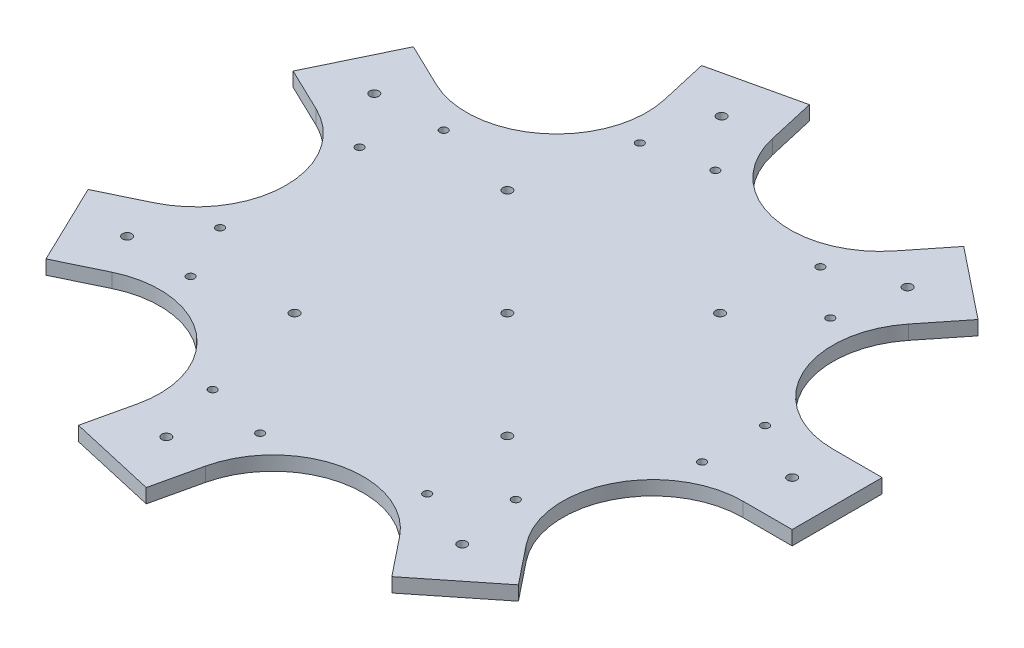
SolidWorks part; units mm, degrees
ref_plane "Front Plane" through (0, 0, 0) normal (0, 0, 1) x (1, 0, 0)
ref_plane "Top Plane" through (0, 0, 0) normal (0, 1, 0) x (1, 0, 0)
ref_plane "Right Plane" through (0, 0, 0) normal (1, 0, 0) x (0, 0, -1)
sketch "Sketch2" plane through (0, 0, 0) normal (0, 0, 1) x (1, 0, 0)
  line L0 (0, 0) -> (0, 63.9226) construction
sketch "Sketch3" plane through (0, 0, 0) normal (0, 1, 0) x (1, 0, 0)
  line L0 (0, 31.75) -> (0, -31.75)
  line L1 (0, 31.75) -> (232.55, 31.75)
  line L2 (0, -31.75) -> (232.55, -31.75)
  line L3 (232.55, 31.75) -> (232.55, -31.75)
  line L4 (0, 0) -> (-515.3919, 0) construction
  line L5 (159.525, 22.225) -> (159.525, -22.225) construction
  line L6 (150, 31.75) -> (150, -31.75) construction
  circle A2 centre (200.8, 0) radius 3.25
  circle A3 centre (159.525, 22.225) radius 2.7781
  circle A4 centre (159.525, -22.225) radius 2.7781
  circle A5 centre (159.525, 22.225) radius 6.35 construction
  circle A6 centre (200.8, 0) radius 22.225 construction
  point P3 (0, 0)
  point P14 (159.525, 0)
  dimension "D6" = 9.525
  dimension "D4" = 6.5
  dimension "D7" = 5.5562
  dimension "D8" = 12.7
  dimension "D9" = 44.45
  dimension "D1" = 63.5
  dimension "D2" = 50.8
  dimension "D3" = 150
  dimension "D5" = 9.525
  dimension "D10" = 82.55
extrude "Boss-Extrude1" add sketch "Sketch3" along normal blind 10
pattern_circular "CirPattern1" count 7 every 51.429 about axis through (0, 0, 0) along (0, 1, 0) of "Boss-Extrude1"
fillet "Fillet1" radius 63.5 7 edges at (65.9296, 5, 31.75) (16.2833, 5, 71.3416) (-45.6247, 5, 57.2115) (-73.1763, 5, 0) (-45.6247, 5, -57.2115) (16.2833, 5, -71.3416) (65.9296, 5, -31.75)
ref_plane "Plane1" through (-82.7012, 10, -219.6544) normal (-0.9749, 0, 0.2225) x (0.2225, 0, 0.9749)
sketch "Sketch5" plane through (0, 0, 0) normal (0, 1, 0) x (1, 0, 0)
  line L4 (-75, 75) -> (-75, -75) construction
  line L5 (-75, 75) -> (75, 75) construction
  line L6 (-75, -75) -> (75, -75) construction
  line L7 (75, 75) -> (75, -75) construction
  line L8 (-75, -75) -> (75, 75) construction
  circle A0 centre (-75, 75) radius 3.25
  circle A1 centre (75, 75) radius 3.25
  circle A2 centre (75, -75) radius 3.25
  circle A3 centre (-75, -75) radius 3.25
  circle A4 centre (0, 0) radius 3.25
  point P0 (0, 0)
  dimension "D3" = 6.5
  dimension "D1" = 150
  dimension "D2" = 150
extrude "Cut-Extrude4" cut sketch "Sketch5" along normal through all
